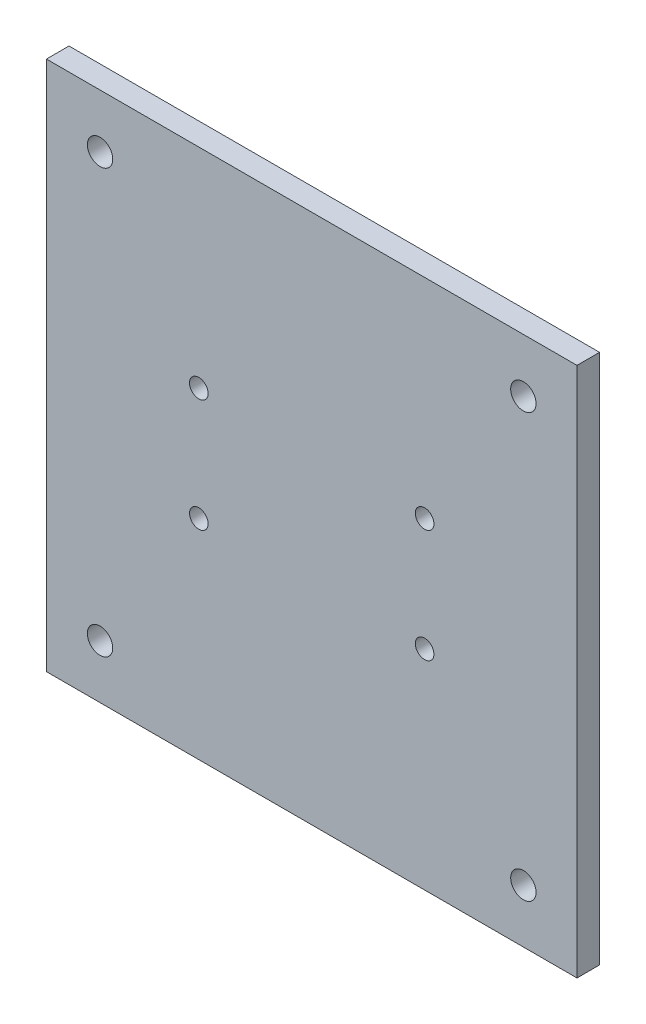
SolidWorks part; units mm, degrees
ref_plane "Front Plane" through (0, 0, 0) normal (0, 0, 1) x (1, 0, 0)
ref_plane "Top Plane" through (0, 0, 0) normal (0, 1, 0) x (1, 0, 0)
ref_plane "Right Plane" through (0, 0, 0) normal (1, 0, 0) x (0, 0, -1)
sketch "Sketch1" plane through (0, 0, 0) normal (0, 0, 1) x (1, 0, 0)
  line L0 (39, 45) -> (39, 0) construction
  line L1 (0, 0) -> (78, 0)
  line L2 (0, 0) -> (0, 45)
  line L3 (0, 45) -> (78, 45)
  line L4 (78, 0) -> (78, 45)
  line L5 (0, 22.5) -> (78, 22.5) construction
  circle A0 centre (19, 32.5) radius 1.6
  circle A1 centre (59, 32.5) radius 1.6
  circle A2 centre (59, 12.5) radius 1.6
  circle A3 centre (19, 12.5) radius 1.6
  dimension "D3" = 3.2
  dimension "D4" = 10
  dimension "D5" = 20
  dimension "D1" = 45
  dimension "D2" = 78
extrude "Boss-Extrude1" add sketch "Sketch1" along normal blind 4
sketch "Sketch5" plane through (0, 0, 0) normal (0, 0, 1) x (1, 0, 0)
  line L0 (-8, 69.5) -> (86, -24.5) construction
  line L1 (-8, 69.5) -> (86, 69.5)
  line L2 (-8, 69.5) -> (-8, -24.5)
  line L3 (-8, -24.5) -> (86, -24.5)
  line L4 (86, 69.5) -> (86, -24.5)
  line L5 (86, 69.5) -> (-8, -24.5) construction
  line L6 (0, 0) -> (78, 0) construction
  line L7 (0, 45) -> (0, 0) construction
  line L9 (-8, 22.5) -> (86, 22.5) construction
  circle A0 centre (1.5, 60) radius 2.25
  circle A1 centre (76.5, 60) radius 2.25
  circle A2 centre (76.5, -15) radius 2.25
  circle A3 centre (1.5, -15) radius 2.25
  dimension "D6" = 4.5
  dimension "D7" = 4.5
  dimension "D8" = 4.5
  dimension "D9" = 4.5
  dimension "D3" = 24.5
  dimension "D1" = 75
  dimension "D2" = 94
  dimension "D4" = 8
extrude "Boss-Extrude3" add sketch "Sketch5" along normal blind 4
sketch "Sketch6" plane through (0, 0, 0) normal (0, 0, -1) x (-1, 0, 0)
  line L0 (-39, 69.5) -> (-39, -24.5) construction
  line L1 (-86, 69.5) -> (8, 69.5) construction
  line L2 (8, -24.5) -> (-86, -24.5) construction
  line L3 (-86, 22.5) -> (8, 22.5) construction
  line L4 (-86, -24.5) -> (-86, 69.5) construction
  line L5 (8, 69.5) -> (8, -24.5) construction
  circle A0 centre (-59, 32.5) radius 1.65
  circle A1 centre (-59, 12.5) radius 1.65
  circle A2 centre (-19, 12.5) radius 1.65
  circle A3 centre (-19, 32.5) radius 1.65
  dimension "D1" = 3.3
  dimension "D2" = 20
  dimension "D3" = 10
extrude "Cut-Extrude1" cut sketch "Sketch6" against normal through all
chamfer "Chamfer1" distance 1.6 angle 45 4 edges at (20.65, 32.5, 0) (17.35, 12.5, 0) (57.35, 32.5, 0) (60.65, 12.5, 0)
